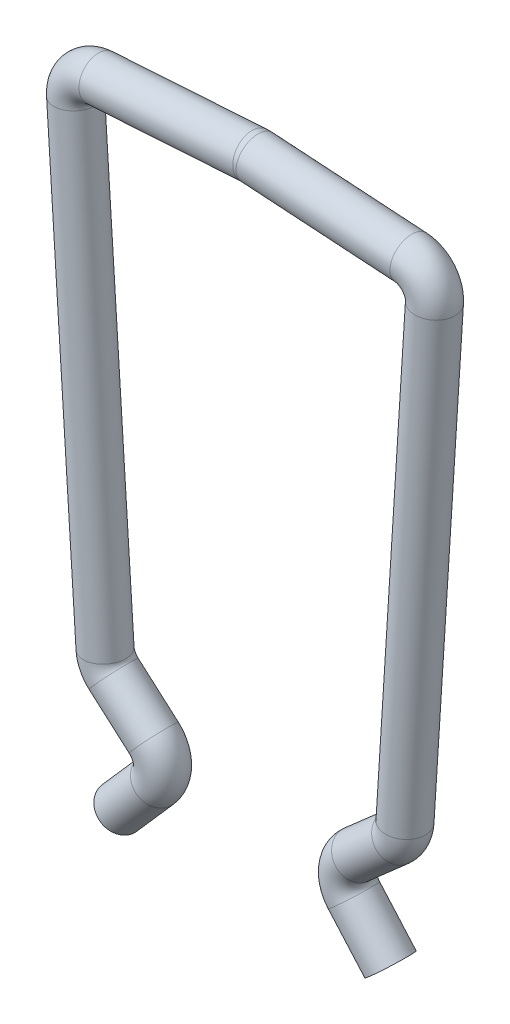
SolidWorks part; units mm, degrees
ref_plane "Front Plane" through (0, 0, 0) normal (0, 0, 1) x (1, 0, 0)
ref_plane "Top Plane" through (0, 0, 0) normal (0, 1, 0) x (1, 0, 0)
ref_plane "Right Plane" through (0, 0, 0) normal (1, 0, 0) x (0, 0, -1)
sketch "Sketch1" plane through (0, 0, 0) normal (0, 0, 1) x (1, 0, 0)
  line L0 (-0.0064, -0.0004) -> (-3.0003, -0.1936)
  line L1 (-3.0937, -0.2997) -> (-2.5197, -9.3401)
  line L2 (-2.4859, -9.4089) -> (-1.7059, -10.0944)
  line L3 (-1.624, -11.3645) -> (-2.3368, -12.1757)
  line L4 (-2.3, -10.7704) -> (-2.987, -10.8147) construction
  line L5 (0, 0) -> (0, -12.2414) construction
  line L6 (-3.3549, -12.2414) -> (-1.7318, -12.1367) construction
  line L7 (0.0064, -0.0004) -> (3.0003, -0.1936)
  line L8 (3.3549, -12.2414) -> (1.7318, -12.1367) construction
  line L9 (2.3, -10.7704) -> (2.987, -10.8147) construction
  line L10 (1.624, -11.3645) -> (2.3368, -12.1757)
  line L11 (2.4859, -9.4089) -> (1.7059, -10.0944)
  line L12 (3.0937, -0.2997) -> (2.5197, -9.3401)
  line L13 (-3.9435, -9.4735) -> (-2.167, -9.3589) construction
  arc A0 (-1.624, -11.3645) -> (-1.7059, -10.0944) centre (-2.3, -10.7704) ccw
  arc A1 (1.624, -11.3645) -> (1.7059, -10.0944) centre (2.3, -10.7704) cw
  arc A2 (2.5197, -9.3401) -> (2.4859, -9.4089) centre (2.4199, -9.3338) cw
  arc A3 (3.0937, -0.2997) -> (3.0003, -0.1936) centre (2.9939, -0.2934) ccw
  arc A4 (0.0064, -0.0004) -> (-0.0064, -0.0004) centre (0, -0.1002) ccw
  arc A5 (-3.0937, -0.2997) -> (-3.0003, -0.1936) centre (-2.9939, -0.2934) cw
  arc A6 (-2.4859, -9.4089) -> (-2.5197, -9.3401) centre (-2.4199, -9.3338) cw
  point P23 (2.5171, -9.3815)
  point P26 (3.1, -0.2)
  point P32 (-3.1, -0.2)
  point P35 (-2.5171, -9.3815)
  dimension "D4" = 45
  dimension "D5" = 45
  dimension "D6" = 10.6
  dimension "D8" = 6.2
  dimension "D10" = 0.1
  dimension "D11" = 2.8
  dimension "D7" = 0.9
  dimension "D2" = 0.2
  dimension "D3" = 9.2
  dimension "D9" = 12
ref_plane "Plane1" through (-2.3368, -12.1757, 0) normal (-0.6601, -0.7512, 0) x (-0.7512, 0.6601, 0)
sketch "Sketch2" plane through (-2.3368, -12.1757, 0) normal (-0.6601, -0.7512, 0) x (-0.7512, 0.6601, 0)
  line L0 (0, 0) -> (0.465, 0) construction
  circle A0 centre (0.4, 0) radius 0.4
  dimension "D1" = 0.8
sweep "Sweep2" add profiles "Sketch2" path "Sketch1"
